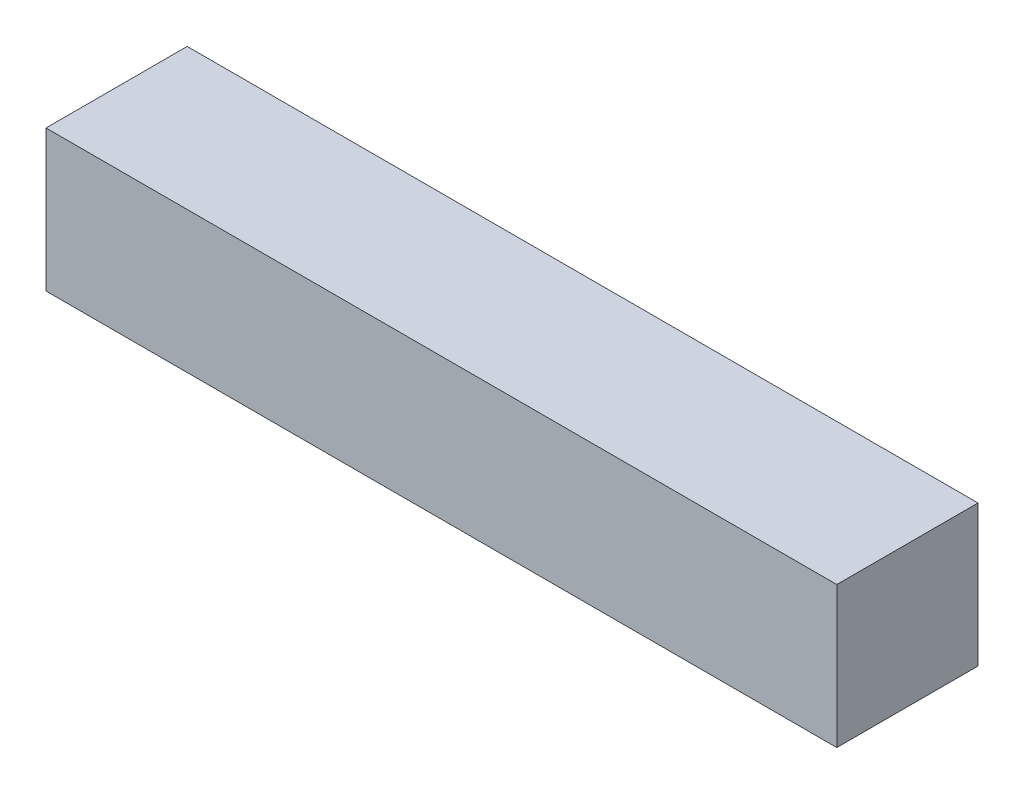
SolidWorks part; units mm, degrees
ref_plane "Front Plane" through (0, 0, 0) normal (0, 0, 1) x (1, 0, 0)
ref_plane "Top Plane" through (0, 0, 0) normal (0, 1, 0) x (1, 0, 0)
ref_plane "Right Plane" through (0, 0, 0) normal (1, 0, 0) x (0, 0, -1)
sketch "Sketch1" plane through (0, 0, 0) normal (0, 1, 0) x (1, 0, 0)
  line L1 (70, -12.5) -> (-70, -12.5)
  line L2 (70, -12.5) -> (70, 12.5)
  line L3 (70, 12.5) -> (-70, 12.5)
  line L4 (-70, -12.5) -> (-70, 12.5)
  line L5 (70, -12.5) -> (-70, 12.5) construction
  line L6 (70, 12.5) -> (-70, -12.5) construction
  point P0 (0, 0)
  point P5 (-70, 0)
  dimension "D1" = 140
  dimension "D2" = 25
extrude "Boss-Extrude1" add sketch "Sketch1" along normal blind 25
sketch "Sketch2" plane through (0, 0, 12.5) normal (0, 0, 1) x (1, 0, 0)
  line L0 (-70, 22.8376) -> (70, 22.8376)
  line L1 (-70, 25) -> (-70, 0) construction
  line L2 (70, 25) -> (70, 0) construction
  spline S0 degree 2 poles (-70, 12.5) (0, 10.0003) (70, 12.5) knots 0 0 0 1 1 1
  point P8 (-500000, 60752.5992)
sketch "Sketch3" plane through (-70, 0, 0) normal (-1, 0, 0) x (0, 0, 1)
  line L0 (12.5, 25) -> (-12.5, 0)
  line L1 (-12.5, 25) -> (12.5, 0)
  circle A0 centre (0, 12.5) radius 12.5
  point P10 (14.9425, 56.9827)
sketch "Sketch4" plane through (70, 0, 0) normal (1, 0, 0) x (0, 0, -1)
  line L0 (12.5, 25) -> (-12.5, 0)
  line L1 (-12.5, 25) -> (12.5, 0)
  circle A0 centre (0, 12.5) radius 12.4007
  point P10 (-7.4057, 0.9787)
sketch "Sketch5" plane through (0, 0, 12.5) normal (0, 0, 1) x (1, 0, 0)
  line L0 (30, 23.3673) -> (30, 19.8673)
  line L1 (-70, 25) -> (70, 25)
  line L2 (-50, 24.0204) -> (-50, 20.5204)
  line L3 (-70, 25) -> (70, 25) construction
  line L4 (-50, 20.5204) -> (-50, 1.0204)
  line L5 (30, 25) -> (-50, 25)
  line L6 (0, 11.2502) -> (0, 25)
  line L7 (-70, 21.5) -> (-50, 21.5)
  line L8 (0, 11.2502) -> (0, 14.7502)
  line L9 (-70, 25) -> (-70, 21.5)
  line L10 (-50, 1.0204) -> (-50, 4.813)
  line L11 (-70, 0) -> (-70, 2)
  line L12 (-70, 2) -> (-70, 0)
  line L13 (-70, 0) -> (70, 0)
  line L14 (70, 0) -> (70, 2)
  line L15 (0, 23) -> (0, 19.5)
  line L16 (30, 23.3673) -> (30, 0.3673)
  line L17 (30, 0.3673) -> (30, 3.8673)
  line L18 (0, 0) -> (0, 3.5)
  spline S0 degree 2 poles (-70, 25) (0, 21) (70, 25) knots 0 0 0 1 1 1
  spline S1 degree 2 poles (-70, 2) (0, -2) (70, 2) knots 0 0 0 1 1 1
  spline S2 degree 2 poles (-50, 20.5204) (-10.0053, 18.8878) (30, 19.8673) knots 0 0 0 1 1 1
  spline S3 degree 2 poles (-50, 4.813) (-10.0108, 2.8) (30, 3.8673) knots 0 0 0 1 1 1
  point P34 (0, 0)
  dimension "D1" = 3.5
  dimension "D2" = 3.5
  dimension "D3" = 3.5
  dimension "D4" = 3.5
  dimension "D5" = 3.5
  dimension "D6" = 3.5
  dimension "D7" = 3.5
  dimension "D8" = 3.5
